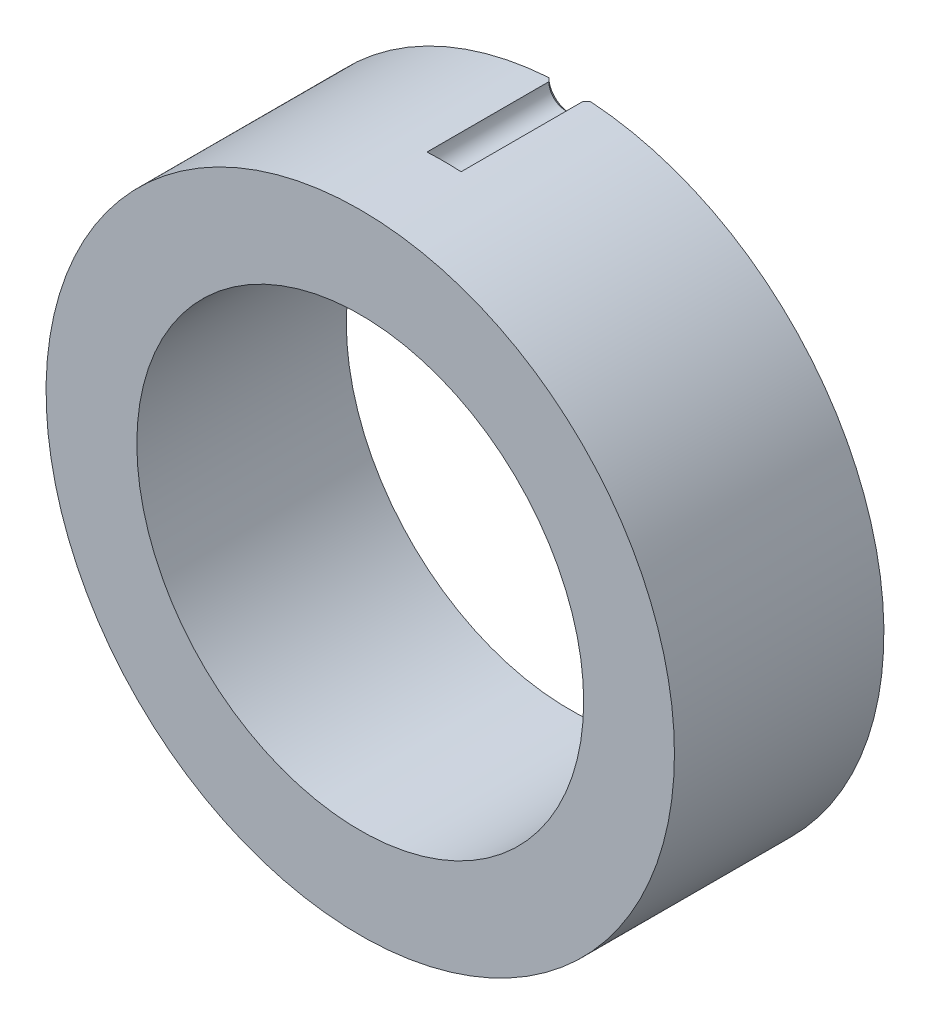
SolidWorks part; units mm, degrees
material "Сталь"
ref_plane "Спереди" through (0, 0, 0) normal (0, 0, 1) x (1, 0, 0)
ref_plane "Сверху" through (0, 0, 0) normal (0, 1, 0) x (1, 0, 0)
ref_plane "Справа" through (0, 0, 0) normal (1, 0, 0) x (0, 0, -1)
sketch "Эскиз1" plane through (0, 0, 0) normal (0, 0, 1) x (1, 0, 0)
  circle A0 centre (0, 0) radius 45
  circle A1 centre (0, 0) radius 32
  dimension "D1" = 90
  dimension "D2" = 64
extrude "Бобышка-Вытянуть1" add sketch "Эскиз1" along normal blind 30
sketch "Эскиз2" plane through (0, 0, 0) normal (0, 0, -1) x (-1, 0, 0)
  circle A0 centre (0, 45) radius 2.4455
  circle A1 centre (0, 0) radius 45 construction
  dimension "D1" = 4.891
extrude "Вырез-Вытянуть1" cut sketch "Эскиз2" against normal blind 18
cosmetic thread "Условное изображение резьбы1" parameters "D2"=6
chamfer "Фаска1" distance 0.5545 angle 45 1 edges at (0, 42.5545, 0)
